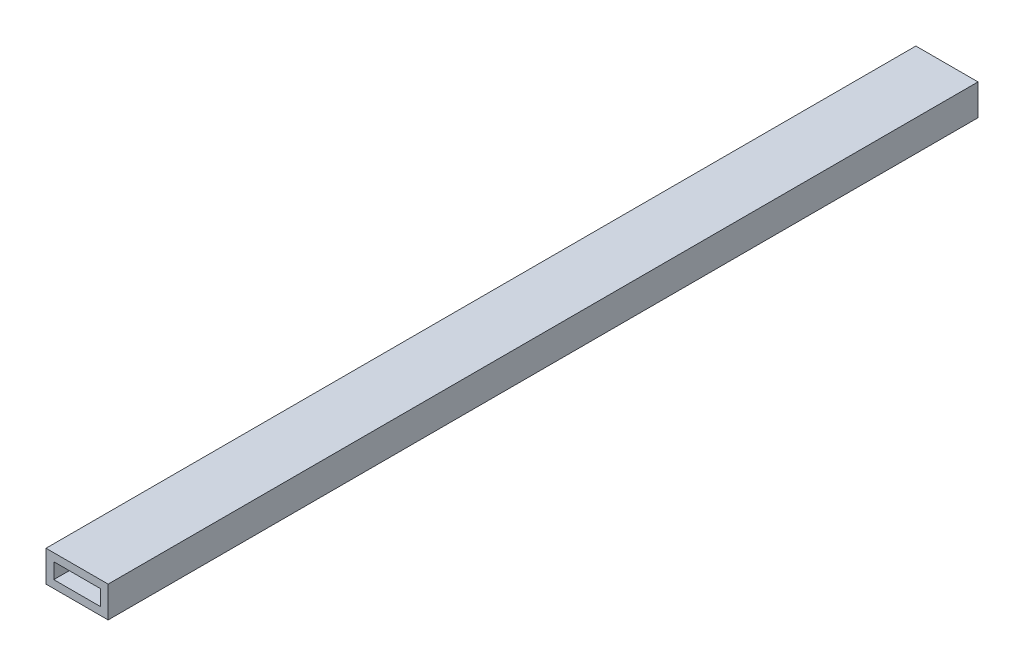
SolidWorks part; units mm, degrees
material "6063-T6"
ref_plane "Front" through (0, 0, 0) normal (0, 0, 1) x (1, 0, 0)
ref_plane "Top" through (0, 0, 0) normal (0, 1, 0) x (1, 0, 0)
ref_plane "Right" through (0, 0, 0) normal (1, 0, 0) x (0, 0, -1)
sketch "Sketch1" plane through (0, 0, 0) normal (0, 0, 1) x (1, 0, 0)
  line L0 (3.175, 9.525) -> (22.225, 9.525)
  line L1 (0, 0) -> (25.4, 0)
  line L2 (0, 0) -> (0, 12.7)
  line L3 (0, 12.7) -> (25.4, 12.7)
  line L4 (25.4, 0) -> (25.4, 12.7)
  line L5 (0, 0) -> (25.4, 12.7) construction
  line L6 (0, 12.7) -> (25.4, 0) construction
  line L7 (22.225, 3.175) -> (22.225, 9.525)
  line L8 (3.175, 3.175) -> (22.225, 3.175)
  line L9 (3.175, 3.175) -> (3.175, 9.525)
  point P4 (12.7, 6.35)
  dimension "D1" = 12.7
  dimension "D2" = 25.4
  dimension "D3" = 3.175
extrude "Boss-Extrude1" add sketch "Sketch1" along normal blind 355.6
